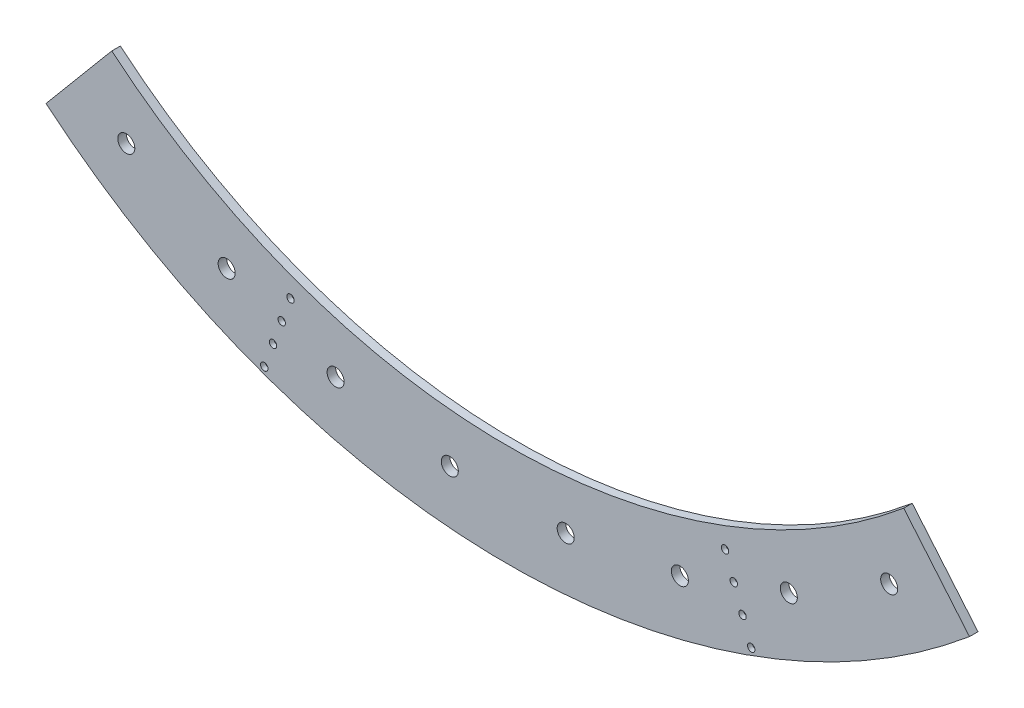
SolidWorks part; units mm, degrees
material "6061-T6 Al"
ref_plane "Front" through (0, 0, 0) normal (0, 0, 1) x (1, 0, 0)
ref_plane "Top" through (0, 0, 0) normal (0, 1, 0) x (1, 0, 0)
ref_plane "Right" through (0, 0, 0) normal (1, 0, 0) x (0, 0, -1)
sketch "Sketch" plane through (0, 0, 0) normal (0, 0, 1) x (1, 0, 0)
  line L0 (418.6457, -897.7885) -> (387.784, -831.6054) construction
  line L1 (0, -1069.975) -> (0, -917.575) construction
  line L2 (256.3861, -956.8461) -> (237.4859, -886.3094) construction
  line L3 (86.3365, -986.8305) -> (79.9719, -914.0834) construction
  line L7 (589.8058, -702.9032) -> (687.7667, -819.6484)
  line L8 (-589.8058, -702.9032) -> (-687.7667, -819.6484)
  line L9 (568.1848, -811.452) -> (526.2994, -751.6334) construction
  arc A21 (0, -990.6) -> (568.1848, -811.452) centre (0, 0) ccw construction
  arc A22 (-589.8058, -702.9032) -> (589.8058, -702.9032) centre (0, 0) ccw
  arc A23 (-687.7667, -819.6484) -> (687.7667, -819.6484) centre (0, 0) ccw
  point P5 (-25.908, 20.828)
  point P6 (25.908, 20.828)
  point P7 (25.908, -20.828)
  point P8 (-25.908, -20.828)
  point P63 (-25.781, -19.05)
  point P64 (25.781, -19.05)
  dimension "D6" = 80
  dimension "D7" = 152.4
  dimension "D3" = 35
  dimension "D4" = 4
  dimension "D1" = 990.6
  dimension "D2" = 917.575
extrude "Boss-Extrude1" add sketch "Sketch" along normal blind 12.7
hole_wizard "1 (1) Diameter Hole1" positions "Sketch5" profile "Sketch4" hole size "1" standard "ANSI Inch" end condition through all
sketch "Sketch5" plane through (0, 0, 12.7) normal (0, 0, 1) x (1, 0, 0)
  line L0 (0, -1069.975) -> (0, -917.575) construction
  line L1 (0, -1069.975) -> (0, -917.575) construction
  point P0 (568.1848, -811.452)
  point P2 (-418.6457, -897.7885)
  point P4 (418.6457, -897.7885)
  point P6 (-568.1848, -811.452)
  point P30 (256.3861, -956.8461)
  point P33 (86.3365, -986.8305)
  point P38 (-86.3365, -986.8305)
  point P40 (-256.3861, -956.8461)
sketch "Sketch4" plane through (568.1848, -811.452, 12.7) normal (1, 0, 0) x (0, -1, 0)
  line L0 (0, 0) -> (0, 12.7)
  line L1 (0, 12.7) -> (12.7, 12.7)
  line L2 (12.7, 12.7) -> (12.7, 0)
  line L5 (12.7, 0) -> (0, 0)
  line L11 (0, -6.35) -> (0, 107.95) construction
  dimension "Thru Hole Dia." = 25.4
  dimension "Thru Hole Depth" = 12.7
hole_wizard "CBORE for 1/4 Socket Head Cap Screw1" positions "Sketch7" profile "Sketch6" counterbore size "1/4" standard "ANSI Inch" end condition through all
sketch "Sketch7" plane through (11.7112, 16.2291, 12.7) normal (0, 0, -1) x (-1, 0, 0)
  line L2 (-350.9841, -1012.7261) -> (-344.4686, -994.825) construction
  line L3 (-324.9222, -941.1215) -> (-318.4067, -923.2204) construction
  line L4 (-337.9531, -976.9238) -> (-331.4377, -959.0227) construction
  line L5 (-318.4067, -923.2204) -> (-311.8912, -905.3192) construction
  line L6 (-331.4377, -959.0227) -> (-324.9222, -941.1215) construction
  line L7 (-344.4686, -994.825) -> (-337.9531, -976.9238) construction
  line L9 (-676.0555, -835.8775) -> (-578.0947, -719.1323) construction
  line L10 (11.7112, -1086.2041) -> (11.7112, -933.8041) construction
  line L11 (11.7112, -1086.2041) -> (11.7112, -933.8041) construction
  arc A0 (-627.0751, -777.5049) -> (11.7112, -1010.0041) centre (11.7112, -16.2291) ccw construction
  point P0 (-350.9841, -1012.7261)
  point P2 (-324.9222, -941.1215)
  point P5 (-311.8912, -905.3192)
  point P18 (-337.9531, -976.9238)
  point P64 (335.3135, -905.3192)
  point P66 (348.3445, -941.1215)
  point P68 (361.3755, -976.9238)
  point P70 (374.4064, -1012.7261)
  dimension "D1" = 114.3
  dimension "D2" = 20
  dimension "D3" = 946.15
sketch "Sketch6" plane through (362.6953, -996.497, 12.7) normal (1, 0, 0) x (0, -1, 0)
  line L0 (0, 0) -> (0, 12.7)
  line L1 (0, 12.7) -> (3.2639, 12.7)
  line L3 (3.2639, 12.7) -> (3.2639, 7.112)
  line L4 (3.2639, 7.112) -> (5.5562, 7.112)
  line L5 (5.5562, 7.112) -> (5.5562, 0)
  line L7 (5.5562, 0) -> (0, 0)
  line L11 (0, -6.35) -> (0, 107.95) construction
  dimension "Thru Hole Dia." = 6.5278
  dimension "Thru Hole Depth" = 12.7
  dimension "C'Bore Dia." = 11.1125
  dimension "C'Bore Depth" = 7.112
